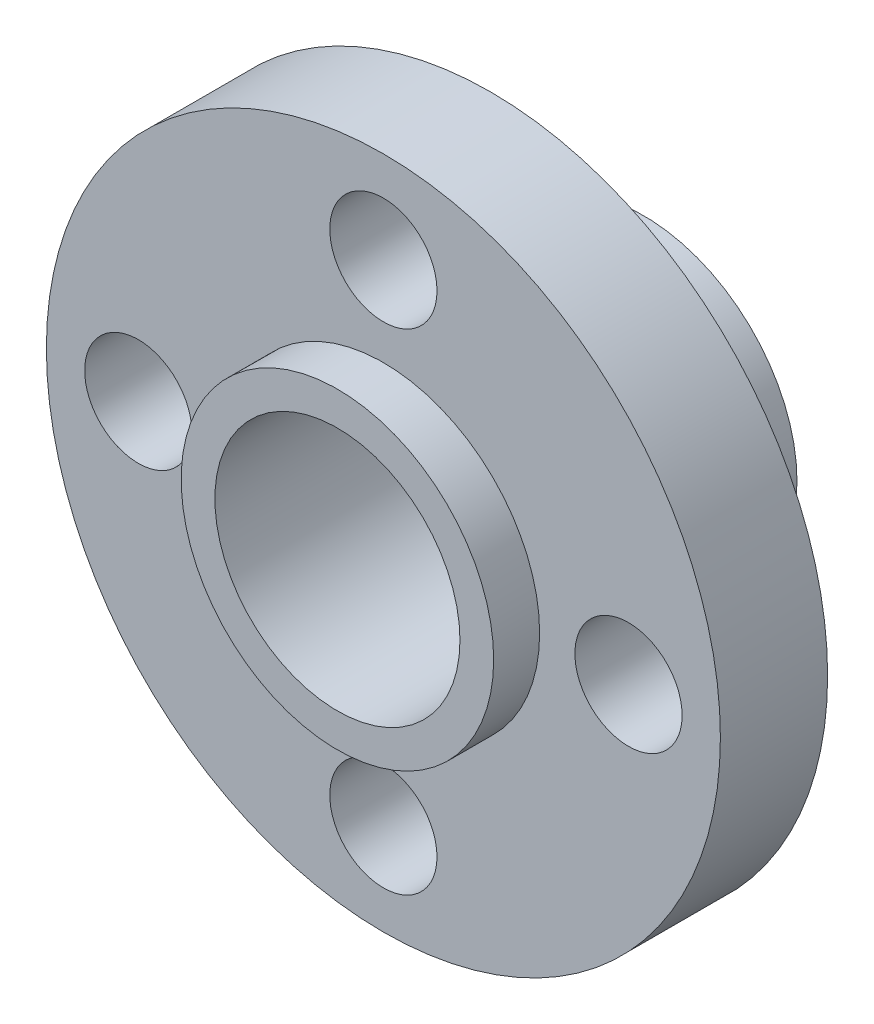
SolidWorks part; units mm, degrees
material "黃銅"
ref_plane "前基準面" through (0, 0, 0) normal (0, 0, 1) x (1, 0, 0)
ref_plane "上基準面" through (0, 0, 0) normal (0, 1, 0) x (1, 0, 0)
ref_plane "右基準面" through (0, 0, 0) normal (1, 0, 0) x (0, 0, -1)
sketch "草圖1" plane through (0, 0, 0) normal (0, 0, 1) x (1, 0, 0)
  line L0 (-11, 0) -> (11, 0) construction
  line L1 (0, 11) -> (0, -11) construction
  circle A0 centre (0, 0) radius 11
  circle A2 centre (0, 8) radius 1.75
  circle A3 centre (8, 0) radius 1.75
  circle A4 centre (0, -8) radius 1.75
  circle A5 centre (-8, 0) radius 1.75
  point P7 (0, 0)
  point P10 (0, 0)
  point P21 (0, 0)
  dimension "D1" = 22
  dimension "D3" = 8
  dimension "D4" = 3.5
  dimension "D6" = 8
  dimension "D7" = 8
  dimension "D5" = 4
extrude "填料-伸長2" add sketch "草圖1" along normal blind 3.5
sketch "草圖2" plane through (0, 0, 3.5) normal (0, 0, 1) x (1, 0, 0)
  circle A0 centre (0, 0) radius 5.1
extrude "填料-伸長4" add sketch "草圖2" along normal blind 1.5
sketch "草圖3" plane through (0, 0, 0) normal (0, 0, -1) x (-1, 0, 0)
  circle A0 centre (0, 0) radius 5
  dimension "D1" = 10
extrude "填料-伸長5" add sketch "草圖3" along normal blind 5
sketch "草圖4" plane through (0, 0, 5) normal (0, 0, 1) x (1, 0, 0)
  circle A0 centre (0, 0) radius 4
extrude "除料-伸長4" cut sketch "草圖4" against normal through all
